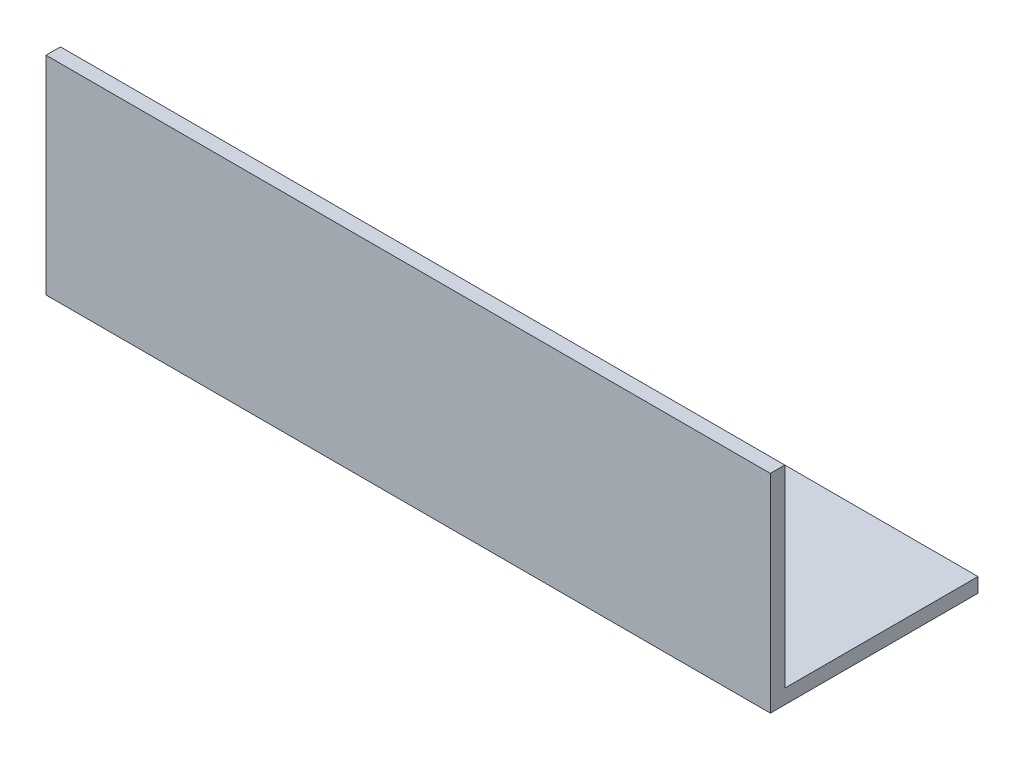
SolidWorks part; units mm, degrees
ref_plane "Спереди" through (0, 0, 0) normal (0, 0, 1) x (1, 0, 0)
ref_plane "Сверху" through (0, 0, 0) normal (0, 1, 0) x (1, 0, 0)
ref_plane "Справа" through (0, 0, 0) normal (1, 0, 0) x (0, 0, -1)
sketch "Эскиз1" plane through (0, 0, 0) normal (1, 0, 0) x (0, 0, -1)
  line L0 (0, 40) -> (0, 0)
  line L1 (0, 0) -> (40, 0)
extrude "Вытянуть-Тонкостенный1" add sketch "Эскиз1" along normal blind 150 thin
